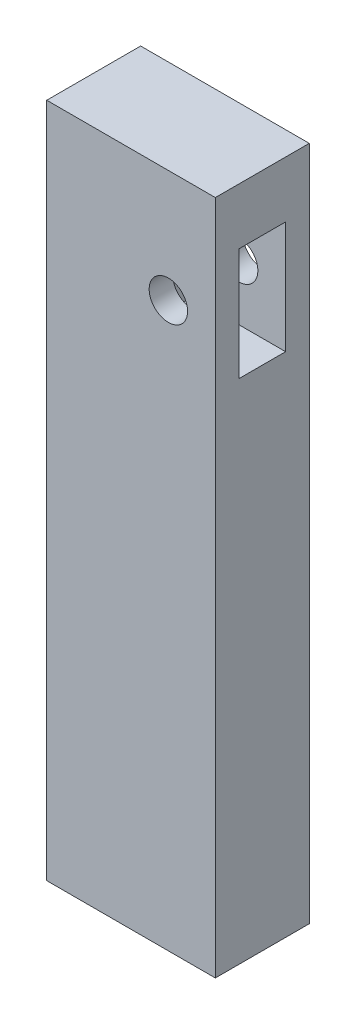
SolidWorks part; units mm, degrees
ref_plane "Front Plane" through (0, 0, 0) normal (0, 0, 1) x (1, 0, 0)
ref_plane "Top Plane" through (0, 0, 0) normal (0, 1, 0) x (1, 0, 0)
ref_plane "Right Plane" through (0, 0, 0) normal (1, 0, 0) x (0, 0, -1)
sketch "Sketch3" plane through (0, 0, 0) normal (0, 0, 1) x (1, 0, 0)
  line L1 (-114, 457) -> (114, 457)
  line L2 (-114, 457) -> (-114, -457)
  line L3 (-114, -457) -> (114, -457)
  line L4 (114, 457) -> (114, -457)
  line L5 (-114, 457) -> (114, -457) construction
  line L6 (-114, -457) -> (114, 457) construction
  point P0 (0, 0)
  dimension "D1" = 914
  dimension "D2" = 228
extrude "Boss-Extrude2" add sketch "Sketch3" along normal blind 127
sketch "Sketch4" plane through (114, 0, 0) normal (1, 0, 0) x (0, 0, -1)
  line L3 (-95, 381) -> (-32, 381)
  line L4 (-95, 381) -> (-95, 229)
  line L5 (-95, 229) -> (-32, 229)
  line L6 (-32, 381) -> (-32, 229)
  line L7 (-95, 381) -> (-32, 229) construction
  line L8 (-95, 229) -> (-32, 381) construction
  dimension "D1" = 152
  dimension "D2" = 63
extrude "Cut-Extrude1" cut sketch "Sketch4" against normal blind 127
sketch "Sketch6" plane through (0, 0, 0) normal (0, 0, 1) x (1, 0, 0)
  line L0 (50.5, 457) -> (50.5, 305)
  line L1 (114, 457) -> (-114, 457) construction
  circle A0 centre (50.5, 305) radius 26
  dimension "D1" = 52
extrude "Cut-Extrude2" cut sketch "Sketch6" along normal blind 127
